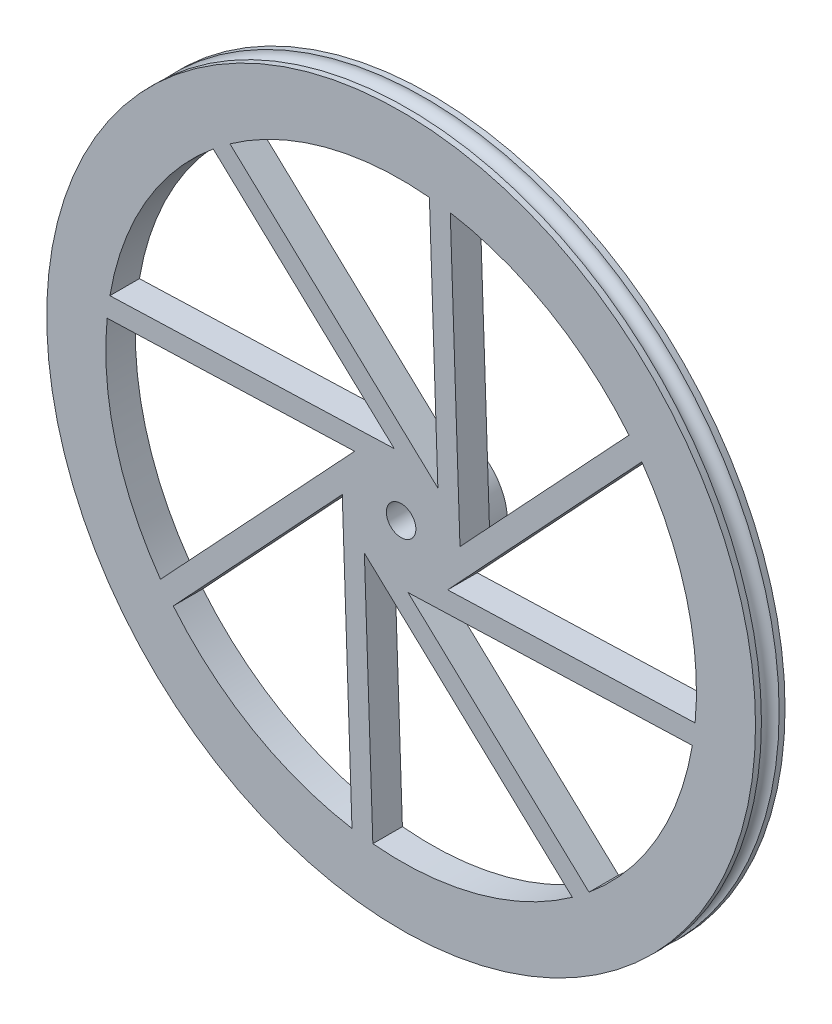
SolidWorks part; units mm, degrees
ref_plane "Front Plane" through (0, 0, 0) normal (0, 0, 1) x (1, 0, 0)
ref_plane "Top Plane" through (0, 0, 0) normal (0, 1, 0) x (1, 0, 0)
ref_plane "Right Plane" through (0, 0, 0) normal (1, 0, 0) x (0, 0, -1)
sketch "Sketch1" plane through (0, 0, 0) normal (0, 0, 1) x (1, 0, 0)
  circle A0 centre (0, 0) radius 60
  point P3 (0, 0)
  dimension "D1" = 120
extrude "Boss-Extrude1" add sketch "Sketch1" against normal blind 5 contours A0
sketch "Sketch6" plane through (0, 0, 0) normal (0, 1, 0) x (1, 0, 0)
  line L0 (60, 0) -> (60, 5) construction
  line L1 (5, 14.4799) -> (50, 14.4799)
  line L2 (5, 14.4799) -> (5, -9.1816)
  line L3 (5, -9.1816) -> (50, -9.1816)
  line L4 (50, 14.4799) -> (50, -9.1816)
  dimension "D1" = 5
  dimension "D2" = 10
ref_axis "Axis1" through (0, 0, -92.1481) along (0, 0, 1)
sketch "Sketch7" plane through (0, 0, 0) normal (0, 0, 1) x (1, 0, 0)
  line L0 (1.1353, -9.9354) -> (31.8083, -38.5776)
  line L1 (0.3422, -9.9941) -> (49.3033, -8.3179)
  line L2 (49.3033, -8.3179) -> (0.3422, -9.9941)
  line L3 (7.8281, -6.2226) -> (49.7704, -4.7866)
  line L4 (-6.825, -7.3089) -> (28.9811, -40.7443)
  line L5 (-6.2226, -7.8281) -> (-4.7866, -49.7704)
  line L6 (-9.9941, -0.3422) -> (-8.3179, -49.3033)
  line L7 (-9.9354, -1.1353) -> (-38.5776, -31.8083)
  line L8 (-7.3089, 6.825) -> (-40.7443, -28.9811)
  line L9 (-7.8281, 6.2226) -> (-49.7704, 4.7866)
  line L10 (-0.3422, 9.9941) -> (-49.3033, 8.3179)
  line L11 (-1.1353, 9.9354) -> (-31.8083, 38.5776)
  line L12 (6.825, 7.3089) -> (-28.9811, 40.7443)
  line L13 (6.2226, 7.8281) -> (4.7866, 49.7704)
  line L14 (9.9941, 0.3422) -> (8.3179, 49.3033)
  line L15 (9.9354, 1.1353) -> (38.5776, 31.8083)
  line L16 (7.3089, -6.825) -> (40.7443, 28.9811)
  line L17 (0, 0) -> (7.8281, -6.2226) construction
  circle A0 centre (0, 0) radius 10
  circle A1 centre (0, 0) radius 50
  dimension "D1" = 20
  dimension "D2" = 100
  dimension "D3" = 8
  dimension "D4" = 10
extrude "Cut-Extrude2" cut sketch "Sketch7" against normal blind 5 contours L5 A1 L4 | L0 A1 L1 | L3 A1 L16 | L15 A1 L14 | L13 A1 L12 | L11 A1 L10 | L9 A1 L8 | L7 A1 L6
sketch "Sketch9" plane through (0, 0, 0) normal (0, 1, 0) x (1, 0, 0)
  line L0 (-60, 5) -> (-60, 0) construction
  circle A0 centre (-60, 2.5) radius 1.5
  dimension "D1" = 3
revolve "Cut-Revolve3" cut sketch "Sketch9" angle 360 about axis through (0, 0, -92.1481) along (0, 0, 1)
sketch "Sketch10" plane through (0, 0, -5) normal (0, 0, -1) x (-1, 0, 0)
  circle A0 centre (0, 0) radius 9
  dimension "D1" = 18
extrude "Boss-Extrude2" add sketch "Sketch10" along normal blind 4
sketch "Sketch11" plane through (0, 0, -9) normal (0, 0, -1) x (-1, 0, 0)
  line L1 (7, 0) -> (3.5, 6.0622)
  line L2 (3.5, 6.0622) -> (-3.5, 6.0622)
  line L3 (-3.5, 6.0622) -> (-7, 0)
  line L4 (-7, 0) -> (-3.5, -6.0622)
  line L5 (-3.5, -6.0622) -> (3.5, -6.0622)
  line L6 (3.5, -6.0622) -> (7, 0)
  circle A0 centre (0, 0) radius 6.0622 construction
  point P1 (0, 0)
  point P10 (0, 0)
  dimension "D1" = 7
extrude "Cut-Extrude4" cut sketch "Sketch11" against normal blind 4
sketch "Sketch12" plane through (0, 0, -5) normal (0, 0, -1) x (-1, 0, 0)
  circle A0 centre (0, 0) radius 2.5
  dimension "D1" = 5
extrude "Cut-Extrude5" cut sketch "Sketch12" against normal through all
